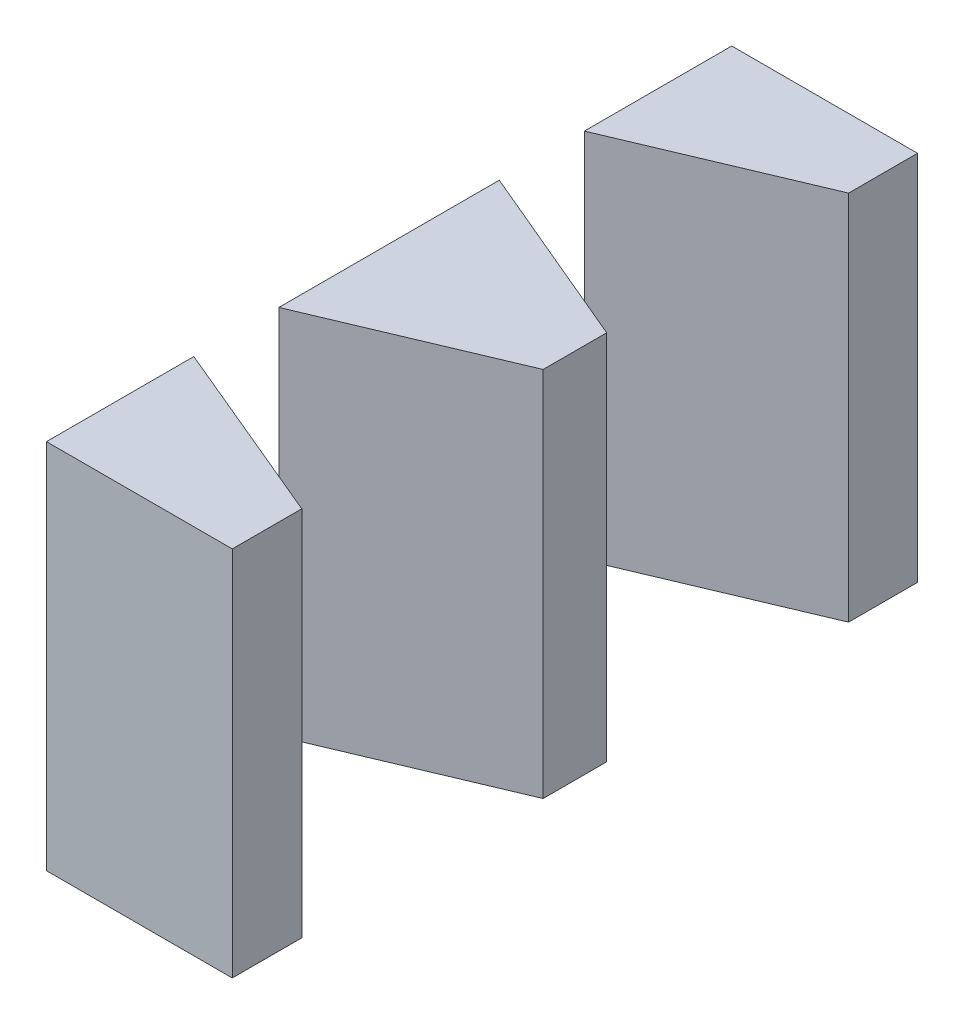
SolidWorks part; units mm, degrees
ref_plane "Front Plane" through (0, 0, 0) normal (0, 0, 1) x (1, 0, 0)
ref_plane "Top Plane" through (0, 0, 0) normal (0, 1, 0) x (1, 0, 0)
ref_plane "Right Plane" through (0, 0, 0) normal (1, 0, 0) x (0, 0, -1)
sketch "Sketch1" plane through (0, 0, 0) normal (0, 1, 0) x (1, 0, 0)
  line L1 (0, 0) -> (7.5, 0)
  line L2 (0, 0) -> (0, 27.66)
  line L3 (0, 27.66) -> (7.5, 27.66)
  line L4 (7.5, 0) -> (7.5, 27.66)
  dimension "D1" = 27.66
  dimension "D2" = 7.5
extrude "Boss-Extrude1" add sketch "Sketch1" along normal blind 25
sketch "Sketch2" plane through (0, 0, 0) normal (0, -1, 0) x (1, 0, 0)
  line L1 (0, 0) -> (7.5, 0)
  line L2 (0, 0) -> (0, -27.66)
  line L3 (0, -27.66) -> (7.5, -27.66)
  line L4 (7.5, 0) -> (7.5, -27.66)
extrude "Cut-Extrude1" cut sketch "Sketch2" against normal blind 10
sketch "Sketch3" plane through (0, 10, 0) normal (0, -1, 0) x (1, 0, 0)
  line L0 (0, -6.165) -> (0, -5.9482)
  line L1 (0, -5.9482) -> (7.5, -2.8054)
  line L2 (7.5, -2.8054) -> (7.5, -3.239)
  line L3 (0, -6.165) -> (7.5, -3)
  line L4 (0, 0) -> (0, -27.66) construction
  line L5 (7.5, -27.66) -> (7.5, 0) construction
  line L6 (7.5, -3) -> (7.5, -12.33)
  line L7 (7.5, -12.33) -> (0, -9.165)
  line L8 (0, -9.165) -> (0, -6.165)
  line L9 (0, -18.495) -> (7.5, -15.33)
  line L10 (7.5, -15.33) -> (7.5, -24.66)
  line L11 (7.5, -24.66) -> (0, -21.495)
  line L12 (0, -21.495) -> (0, -18.495)
  line L13 (7.5, -3.239) -> (0, -6.3818)
  line L14 (0, -6.3818) -> (0, -6.165)
  line L15 (7.5, -12.5471) -> (7.5, -12.1129)
  line L16 (7.5, -12.1129) -> (0, -8.9479)
  line L17 (0, -8.9479) -> (0, -9.3821)
  line L18 (0, -9.3821) -> (7.5, -12.5471)
  line L19 (0, -18.2779) -> (7.5, -15.1129)
  line L20 (7.5, -15.1129) -> (7.5, -15.5471)
  line L21 (7.5, -15.5471) -> (0, -18.7121)
  line L22 (0, -18.7121) -> (0, -18.2779)
  line L23 (7.5, -24.4429) -> (0, -21.2779)
  line L24 (0, -21.2779) -> (0, -21.7121)
  line L25 (0, -21.7121) -> (7.5, -24.8771)
  line L26 (7.5, -24.8771) -> (7.5, -24.4429)
  dimension "D1" = 9.33
  dimension "D2" = 9.33
  dimension "D3" = 3
  dimension "D4" = 3
  dimension "D5" = 6.165
  dimension "D6" = 9.33
  dimension "D7" = 3
  dimension "D8" = 3
  dimension "D9" = 0.4
  dimension "D10" = 0.2
  dimension "D12" = 0.4
  dimension "D13" = 0.2
  dimension "D14" = 0.4
  dimension "D15" = 0.2
  dimension "D16" = 0.2
  dimension "D17" = 0.4
extrude "Cut-Extrude2" cut sketch "Sketch3" against normal through all both and the other way through all contours L18 L3 L2 L1 | L13 L16 L3 L18 | L16 L18 L7 | L18 L16 L7 | L19 L18 L9 L16 | L18 L25 L16 L11 | L16 L23 L18 L11
sketch "Sketch4" plane through (0, 10, 0) normal (0, -1, 0) x (1, 0, 0)
  line L0 (0, -18.7121) -> (7.5, -15.5471)
  line L1 (7.5, -24.4429) -> (7.5, -15.5471) construction
  line L2 (7.5, -15.5471) -> (0, -18.7121) construction
  line L3 (7.5, -15.5471) -> (7.5, -24.4429)
  line L4 (7.5, -24.4429) -> (0, -21.2779)
  line L5 (0, -21.2779) -> (0, -18.7121)
  line L6 (0, -6.3818) -> (7.5, -3.239)
  line L7 (7.5, -3.239) -> (7.5, -12.1129)
  line L8 (7.5, -12.1129) -> (0, -8.9479)
  line L9 (0, -8.9479) -> (0, -6.3818)
extrude "Cut-Extrude3" cut sketch "Sketch4" against normal through all both and the other way through all
